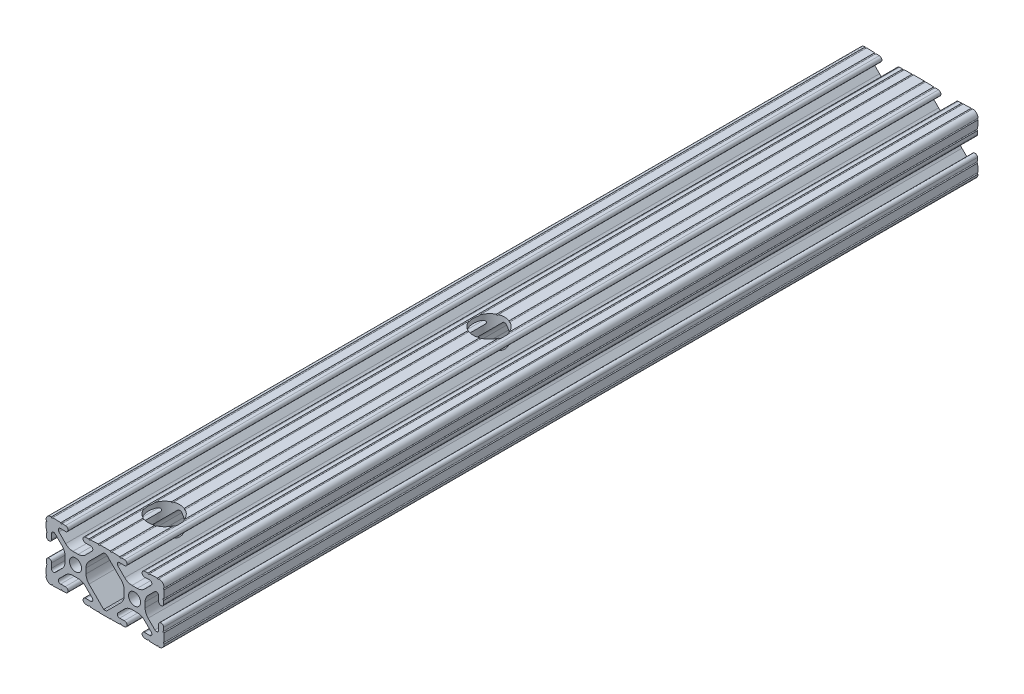
SolidWorks part; units mm, degrees
ref_plane "Front Plane" through (0, 0, 0) normal (0, 0, 1) x (1, 0, 0)
ref_plane "Top Plane" through (0, 0, 0) normal (0, 1, 0) x (1, 0, 0)
ref_plane "Right Plane" through (0, 0, 0) normal (1, 0, 0) x (0, 0, -1)
sketch "Sketch1" plane through (0, 0, 0) normal (0, 0, 1) x (1, 0, 0)
  line L0 (0, 12.7) -> (-12.7814, 12.7) construction
  line L1 (-4.5085, 0) -> (-4.5085, 2.9459)
  line L2 (-6.0437, 12.5461) -> (-10.0976, 12.6876) construction
  line L3 (-11.5616, 12.4229) -> (-4.3159, 12.1699) construction
  line L4 (-6.4364, 10.3486) -> (-6.3592, 12.5571) construction
  line L6 (-2.9459, 4.5085) -> (0, 4.5085)
  line L7 (0, 0) -> (0, 12.7) construction
  line L8 (0, 0) -> (-12.7814, 0) construction
  line L9 (0.7813, 0.7813) -> (-0.7813, -0.7813) construction
  line L10 (-2.9459, 4.5085) -> (-7.1484, 8.711)
  line L11 (-4.5085, 2.9459) -> (-8.711, 7.1484)
  line L13 (0, 0) -> (-12.7814, 12.7814) construction
  line L14 (-10.4131, 12.6987) -> (-4.3048, 12.4853)
  line L15 (-4.3048, 12.4853) -> (-4.382, 10.2769) construction
  line L16 (-4.382, 10.2769) -> (-6.4364, 10.3486)
  line L17 (-12.6987, 10.4131) -> (-12.4853, 4.3048)
  line L18 (-10.2769, 4.382) -> (-10.3486, 6.4364)
  circle A0 centre (0, 0) radius 2.6035
  arc A1 (-4.382, 10.2769) -> (-4.3048, 12.4853) centre (-4.3434, 11.3811) ccw
  arc A2 (-7.1484, 8.711) -> (-6.4364, 10.3486) centre (-6.4698, 9.3896) cw
  arc A3 (-8.711, 7.1484) -> (-10.3486, 6.4364) centre (-9.3896, 6.4698) ccw
  arc A4 (-10.2769, 4.382) -> (-12.4853, 4.3048) centre (-11.3811, 4.3434) cw
  arc A5 (-10.4131, 12.6987) -> (-12.6987, 10.4131) centre (-10.4902, 10.4902) ccw
  arc A6 (-10.4131, 12.6987) -> (-9.7821, 12.6766) centre (-10.0976, 12.6876) ccw
  arc A7 (-6.3592, 12.5571) -> (-5.7282, 12.5351) centre (-6.0437, 12.5461) ccw
  arc A8 (-12.5571, 6.3592) -> (-12.5351, 5.7282) centre (-12.5461, 6.0437) cw
  arc A9 (-12.6987, 10.4131) -> (-12.6766, 9.7821) centre (-12.6876, 10.0976) cw
  dimension "D1" = 5.207
  dimension "D5" = 14.859
  dimension "D9" = 2
  dimension "D2" = 25.4
  dimension "D12" = 0.6314
  dimension "D10" = 2.2098
  dimension "D3" = 9.017
  dimension "D4" = 9.017
  dimension "D6" = 25.4
  dimension "D7" = 6.477
  dimension "D8" = 2.2098
  dimension "D11" = 12.7
sketch "Sketch3" plane through (0, 0, 0) normal (0, 0, 1) x (1, 0, 0)
  line L0 (-2.9459, 4.5085) -> (0, 4.5085) construction
  line L1 (-2.9459, 4.5085) -> (-7.1484, 8.711) construction
  line L2 (-4.382, 10.2769) -> (-6.4364, 10.3486) construction
  line L3 (-10.4131, 12.6987) -> (-4.3048, 12.4853) construction
  line L4 (-4.5085, 0) -> (-4.5085, 2.9459) construction
  line L5 (-4.5085, 2.9459) -> (-8.711, 7.1484) construction
  line L6 (-10.2769, 4.382) -> (-10.3486, 6.4364) construction
  line L7 (-12.6987, 10.4131) -> (-12.4853, 4.3048) construction
  line L8 (-1.1153, 4.5085) -> (1.1153, 4.5085)
  line L9 (-4.2404, 5.803) -> (-7.1484, 8.711)
  line L10 (-4.382, 10.2769) -> (-6.4364, 10.3486)
  line L11 (-9.7821, 12.6766) -> (-6.3592, 12.5571)
  line L12 (-4.5085, -1.1153) -> (-4.5085, 1.1153)
  line L13 (-5.803, 4.2404) -> (-8.711, 7.1484)
  line L14 (-10.2769, 4.382) -> (-10.3486, 6.4364)
  line L15 (-12.6766, 9.7821) -> (-12.5571, 6.3592)
  line L16 (-5.7282, 12.5351) -> (-4.3048, 12.4853)
  line L17 (-12.5351, 5.7282) -> (-12.4853, 4.3048)
  line L18 (0, 0) -> (0, 12.7) construction
  line L19 (0, 0) -> (-12.7814, 0) construction
  line L20 (0, 0) -> (12.7, 0) construction
  line L21 (5.7282, 12.5351) -> (4.3048, 12.4853)
  line L22 (12.7, 10.5674) -> (12.7, 12.6987) construction
  line L23 (10.4131, 12.6987) -> (14.9869, 12.6987)
  line L24 (5.803, 4.2404) -> (12.1093, 10.5467)
  line L25 (4.5085, -1.1153) -> (4.5085, 1.1153)
  line L26 (9.7821, 12.6766) -> (6.3592, 12.5571)
  line L27 (4.382, 10.2769) -> (6.4364, 10.3486)
  line L28 (4.2404, 5.803) -> (7.1484, 8.711)
  line L29 (4.2404, -5.803) -> (7.1484, -8.711)
  line L30 (4.382, -10.2769) -> (6.4364, -10.3486)
  line L31 (9.7821, -12.6766) -> (6.3592, -12.5571)
  line L32 (5.803, -4.2404) -> (12.1093, -10.5467)
  line L33 (12.1093, 10.5467) -> (12.7, 10.5674)
  line L34 (10.4131, -12.6987) -> (14.9869, -12.6987)
  line L35 (5.7282, -12.5351) -> (4.3048, -12.4853)
  line L36 (12.7, -10.5674) -> (12.7, -12.6987) construction
  line L37 (-12.5351, -5.7282) -> (-12.4853, -4.3048)
  line L38 (-5.7282, -12.5351) -> (-4.3048, -12.4853)
  line L39 (-12.6766, -9.7821) -> (-12.5571, -6.3592)
  line L40 (-10.2769, -4.382) -> (-10.3486, -6.4364)
  line L41 (-5.803, -4.2404) -> (-8.711, -7.1484)
  line L42 (-9.7821, -12.6766) -> (-6.3592, -12.5571)
  line L43 (-4.382, -10.2769) -> (-6.4364, -10.3486)
  line L44 (-4.2404, -5.803) -> (-7.1484, -8.711)
  line L45 (-1.1153, -4.5085) -> (1.1153, -4.5085)
  line L46 (12.1093, -10.5467) -> (12.7, -10.5674)
  line L47 (13.2907, -10.5467) -> (12.7, -10.5674)
  line L48 (26.5153, -4.5085) -> (24.2847, -4.5085)
  line L49 (29.6404, -5.803) -> (32.5484, -8.711)
  line L50 (29.782, -10.2769) -> (31.8364, -10.3486)
  line L51 (35.1821, -12.6766) -> (31.7592, -12.5571)
  line L52 (31.203, -4.2404) -> (34.111, -7.1484)
  line L53 (35.6769, -4.382) -> (35.7486, -6.4364)
  line L54 (38.0766, -9.7821) -> (37.9571, -6.3592)
  line L55 (31.1282, -12.5351) -> (29.7048, -12.4853)
  line L56 (37.9351, -5.7282) -> (37.8853, -4.3048)
  line L57 (19.6718, -12.5351) -> (21.0952, -12.4853)
  line L58 (13.2907, 10.5467) -> (12.7, 10.5674)
  line L59 (19.597, -4.2404) -> (13.2907, -10.5467)
  line L60 (15.6179, -12.6766) -> (19.0408, -12.5571)
  line L61 (21.018, -10.2769) -> (18.9636, -10.3486)
  line L62 (21.1596, -5.803) -> (18.2516, -8.711)
  line L63 (21.1596, 5.803) -> (18.2516, 8.711)
  line L64 (21.018, 10.2769) -> (18.9636, 10.3486)
  line L65 (15.6179, 12.6766) -> (19.0408, 12.5571)
  line L66 (20.8915, -1.1153) -> (20.8915, 1.1153)
  line L67 (19.597, 4.2404) -> (13.2907, 10.5467)
  line L68 (19.6718, 12.5351) -> (21.0952, 12.4853)
  line L69 (37.9351, 5.7282) -> (37.8853, 4.3048)
  line L70 (31.1282, 12.5351) -> (29.7048, 12.4853)
  line L71 (38.0766, 9.7821) -> (37.9571, 6.3592)
  line L72 (35.6769, 4.382) -> (35.7486, 6.4364)
  line L73 (31.203, 4.2404) -> (34.111, 7.1484)
  line L74 (29.9085, -1.1153) -> (29.9085, 1.1153)
  line L75 (35.1821, 12.6766) -> (31.7592, 12.5571)
  line L76 (29.782, 10.2769) -> (31.8364, 10.3486)
  line L77 (29.6404, 5.803) -> (32.5484, 8.711)
  line L78 (26.5153, 4.5085) -> (24.2847, 4.5085)
  arc A0 (-10.4131, 12.6987) -> (-9.7821, 12.6766) centre (-10.0976, 12.6876) ccw construction
  arc A1 (-6.4364, 10.3486) -> (-7.1484, 8.711) centre (-6.4698, 9.3896) ccw construction
  arc A2 (-4.382, 10.2769) -> (-4.3048, 12.4853) centre (-4.3434, 11.3811) ccw construction
  arc A3 (-8.711, 7.1484) -> (-10.3486, 6.4364) centre (-9.3896, 6.4698) ccw construction
  arc A4 (-12.4853, 4.3048) -> (-10.2769, 4.382) centre (-11.3811, 4.3434) ccw construction
  arc A5 (-6.3592, 12.5571) -> (-5.7282, 12.5351) centre (-6.0437, 12.5461) ccw construction
  arc A6 (-10.4131, 12.6987) -> (-12.6987, 10.4131) centre (-10.4902, 10.4902) ccw construction
  arc A7 (-12.6766, 9.7821) -> (-12.6987, 10.4131) centre (-12.6876, 10.0976) ccw construction
  arc A8 (-12.5351, 5.7282) -> (-12.5571, 6.3592) centre (-12.5461, 6.0437) ccw construction
  arc A9 (-10.4131, 12.6987) -> (-9.7821, 12.6766) centre (-10.0976, 12.6876) ccw
  arc A10 (-6.4364, 10.3486) -> (-7.1484, 8.711) centre (-6.4698, 9.3896) ccw
  arc A11 (-4.382, 10.2769) -> (-4.3048, 12.4853) centre (-4.3434, 11.3811) ccw
  arc A12 (-8.711, 7.1484) -> (-10.3486, 6.4364) centre (-9.3896, 6.4698) ccw
  arc A13 (-12.4853, 4.3048) -> (-10.2769, 4.382) centre (-11.3811, 4.3434) ccw
  arc A14 (-6.3592, 12.5571) -> (-5.7282, 12.5351) centre (-6.0437, 12.5461) ccw
  arc A15 (-10.4131, 12.6987) -> (-12.6987, 10.4131) centre (-10.4902, 10.4902) ccw
  arc A16 (-12.6766, 9.7821) -> (-12.6987, 10.4131) centre (-12.6876, 10.0976) ccw
  arc A17 (-12.5351, 5.7282) -> (-12.5571, 6.3592) centre (-12.5461, 6.0437) ccw
  arc A18 (-1.1153, 4.5085) -> (-4.2404, 5.803) centre (-1.1153, 8.9281) cw
  arc A19 (4.5085, 1.1153) -> (5.803, 4.2404) centre (8.9281, 1.1153) cw
  arc A20 (1.1153, 4.5085) -> (4.2404, 5.803) centre (1.1153, 8.9281) ccw
  arc A21 (-4.5085, 1.1153) -> (-5.803, 4.2404) centre (-8.9281, 1.1153) ccw
  circle A22 centre (25.4, 0) radius 2.6035
  arc A23 (35.8131, -12.6987) -> (35.1821, -12.6766) centre (35.4976, -12.6876) ccw
  arc A24 (31.8364, -10.3486) -> (32.5484, -8.711) centre (31.8698, -9.3896) ccw
  arc A25 (6.3592, 12.5571) -> (5.7282, 12.5351) centre (6.0437, 12.5461) cw
  arc A26 (29.782, -10.2769) -> (29.7048, -12.4853) centre (29.7434, -11.3811) ccw
  arc A27 (34.111, -7.1484) -> (35.7486, -6.4364) centre (34.7896, -6.4698) ccw
  arc A28 (4.382, 10.2769) -> (4.3048, 12.4853) centre (4.3434, 11.3811) cw
  arc A29 (6.4364, 10.3486) -> (7.1484, 8.711) centre (6.4698, 9.3896) cw
  arc A30 (10.4131, 12.6987) -> (9.7821, 12.6766) centre (10.0976, 12.6876) cw
  arc A31 (10.4131, -12.6987) -> (9.7821, -12.6766) centre (10.0976, -12.6876) ccw
  arc A32 (6.4364, -10.3486) -> (7.1484, -8.711) centre (6.4698, -9.3896) ccw
  arc A33 (4.382, -10.2769) -> (4.3048, -12.4853) centre (4.3434, -11.3811) ccw
  arc A34 (37.8853, -4.3048) -> (35.6769, -4.382) centre (36.7811, -4.3434) ccw
  arc A35 (31.7592, -12.5571) -> (31.1282, -12.5351) centre (31.4437, -12.5461) ccw
  arc A36 (6.3592, -12.5571) -> (5.7282, -12.5351) centre (6.0437, -12.5461) ccw
  arc A37 (35.8131, -12.6987) -> (38.0987, -10.4131) centre (35.8902, -10.4902) ccw
  arc A38 (38.0766, -9.7821) -> (38.0987, -10.4131) centre (38.0876, -10.0976) ccw
  arc A39 (37.9351, -5.7282) -> (37.9571, -6.3592) centre (37.9461, -6.0437) ccw
  arc A40 (-4.5085, -1.1153) -> (-5.803, -4.2404) centre (-8.9281, -1.1153) cw
  arc A41 (1.1153, -4.5085) -> (4.2404, -5.803) centre (1.1153, -8.9281) cw
  arc A42 (4.5085, -1.1153) -> (5.803, -4.2404) centre (8.9281, -1.1153) ccw
  arc A43 (-1.1153, -4.5085) -> (-4.2404, -5.803) centre (-1.1153, -8.9281) ccw
  arc A44 (-12.5351, -5.7282) -> (-12.5571, -6.3592) centre (-12.5461, -6.0437) cw
  arc A45 (-12.6766, -9.7821) -> (-12.6987, -10.4131) centre (-12.6876, -10.0976) cw
  arc A46 (-10.4131, -12.6987) -> (-12.6987, -10.4131) centre (-10.4902, -10.4902) cw
  arc A47 (-6.3592, -12.5571) -> (-5.7282, -12.5351) centre (-6.0437, -12.5461) cw
  arc A48 (-12.4853, -4.3048) -> (-10.2769, -4.382) centre (-11.3811, -4.3434) cw
  arc A49 (-8.711, -7.1484) -> (-10.3486, -6.4364) centre (-9.3896, -6.4698) cw
  arc A50 (-4.382, -10.2769) -> (-4.3048, -12.4853) centre (-4.3434, -11.3811) cw
  arc A51 (-6.4364, -10.3486) -> (-7.1484, -8.711) centre (-6.4698, -9.3896) cw
  arc A52 (-10.4131, -12.6987) -> (-9.7821, -12.6766) centre (-10.0976, -12.6876) cw
  circle A53 centre (0, 0) radius 2.6035 construction
  circle A54 centre (0, 0) radius 2.6035
  arc A55 (26.5153, -4.5085) -> (29.6404, -5.803) centre (26.5153, -8.9281) cw
  arc A56 (20.8915, -1.1153) -> (19.597, -4.2404) centre (16.4719, -1.1153) cw
  arc A57 (24.2847, -4.5085) -> (21.1596, -5.803) centre (24.2847, -8.9281) ccw
  arc A58 (29.9085, -1.1153) -> (31.203, -4.2404) centre (34.3281, -1.1153) ccw
  arc A59 (19.0408, -12.5571) -> (19.6718, -12.5351) centre (19.3563, -12.5461) cw
  arc A60 (21.018, -10.2769) -> (21.0952, -12.4853) centre (21.0566, -11.3811) cw
  arc A61 (18.9636, -10.3486) -> (18.2516, -8.711) centre (18.9302, -9.3896) cw
  arc A62 (14.9869, -12.6987) -> (15.6179, -12.6766) centre (15.3024, -12.6876) cw
  arc A63 (14.9869, 12.6987) -> (15.6179, 12.6766) centre (15.3024, 12.6876) ccw
  arc A64 (18.9636, 10.3486) -> (18.2516, 8.711) centre (18.9302, 9.3896) ccw
  arc A65 (21.018, 10.2769) -> (21.0952, 12.4853) centre (21.0566, 11.3811) ccw
  arc A66 (19.0408, 12.5571) -> (19.6718, 12.5351) centre (19.3563, 12.5461) ccw
  arc A67 (29.9085, 1.1153) -> (31.203, 4.2404) centre (34.3281, 1.1153) cw
  arc A68 (24.2847, 4.5085) -> (21.1596, 5.803) centre (24.2847, 8.9281) cw
  arc A69 (20.8915, 1.1153) -> (19.597, 4.2404) centre (16.4719, 1.1153) ccw
  arc A70 (26.5153, 4.5085) -> (29.6404, 5.803) centre (26.5153, 8.9281) ccw
  arc A71 (37.9351, 5.7282) -> (37.9571, 6.3592) centre (37.9461, 6.0437) cw
  arc A72 (38.0766, 9.7821) -> (38.0987, 10.4131) centre (38.0876, 10.0976) cw
  arc A73 (35.8131, 12.6987) -> (38.0987, 10.4131) centre (35.8902, 10.4902) cw
  arc A74 (31.7592, 12.5571) -> (31.1282, 12.5351) centre (31.4437, 12.5461) cw
  arc A75 (37.8853, 4.3048) -> (35.6769, 4.382) centre (36.7811, 4.3434) cw
  arc A76 (34.111, 7.1484) -> (35.7486, 6.4364) centre (34.7896, 6.4698) cw
  arc A77 (29.782, 10.2769) -> (29.7048, 12.4853) centre (29.7434, 11.3811) cw
  arc A78 (31.8364, 10.3486) -> (32.5484, 8.711) centre (31.8698, 9.3896) cw
  arc A79 (35.8131, 12.6987) -> (35.1821, 12.6766) centre (35.4976, 12.6876) cw
  point P135 (4.5085, 0)
  point P218 (20.8915, 0)
  dimension "D2" = 4.4196
  dimension "D1" = 12.7
extrude "Extrude1" add sketch "Sketch3" along normal blind 350
sketch "Sketch4" plane through (0, 12.6987, 0) normal (0, 1, 0) x (1, 0, 0)
  line L0 (12.7, -350) -> (12.7, -324.6)
  line L1 (14.9869, -350) -> (10.4131, -350) construction
  line L2 (12.7, -324.6) -> (12.7, -184.9)
  circle A0 centre (12.7, -324.6) radius 6.75
  circle A1 centre (12.7, -184.9) radius 6.75
  dimension "D2" = 13.5
  dimension "D4" = 13.5
  dimension "D1" = 25.4
  dimension "D3" = 139.7
extrude "Cut-Extrude2" cut sketch "Sketch4" against normal through all
equation "\"D10@Sketch1\" = \"D8@Sketch1\""
equation "\"D11@Sketch1\" = \"D6@Sketch1\"/2"
equation "\"D12@Sketch1\" = \"D8@Sketch1\"/3.5"
equation "\"D2@Sketch3\" = \"D8@Sketch1\"*2"
